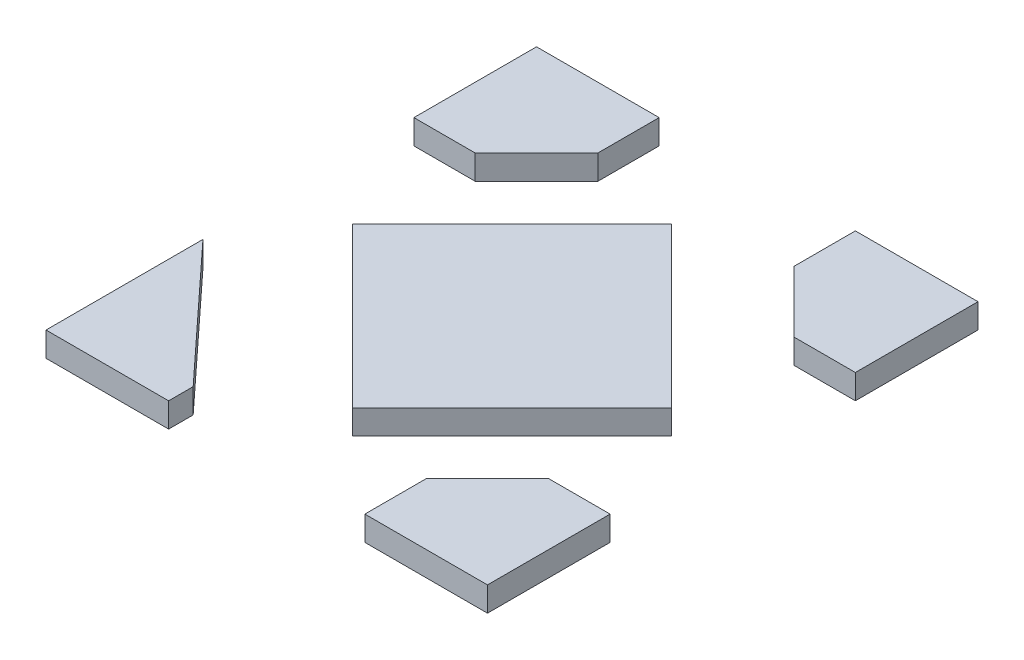
SolidWorks part; units mm, degrees
material "Latón"
ref_plane "Front" through (0, 0, 0) normal (0, 0, 1) x (1, 0, 0)
ref_plane "Top" through (0, 0, 0) normal (0, 1, 0) x (1, 0, 0)
ref_plane "Right" through (0, 0, 0) normal (1, 0, 0) x (0, 0, -1)
sketch "Croquis1" plane through (0, 0, 0) normal (0, -1, 0) x (1, 0, 0)
  line L0 (0.325, -0.6867) -> (-0.325, -0.6867) construction
  line L1 (-0.7516, 0.325) -> (-0.7516, -0.325) construction
  line L2 (-0.7516, -0.325) -> (2.8473, -0.325) construction
  line L3 (-0.7516, 0.325) -> (2.8473, 0.325) construction
  line L4 (0.325, -0.6867) -> (0.325, 1.4562) construction
  line L5 (-0.325, -0.6867) -> (-0.325, 1.4562) construction
  line L6 (0, -0.325) -> (0.325, 0)
  line L7 (0.325, 0) -> (0, 0.325)
  line L8 (0, 0.325) -> (-0.325, 0)
  line L9 (-0.325, 0) -> (0, -0.325)
  point P3 (0, -0.6867)
  point P6 (-0.7516, 0)
  dimension "D1" = 0.65
  dimension "D2" = 0.65
extrude "Saliente-Extruir1" add sketch "Croquis1" along normal blind 0.05
sketch "Croquis2" plane through (0, 0, 0) normal (0, -1, 0) x (1, 0, 0)
  line L0 (0.325, 0) -> (0.325, 0.8942) construction
  line L1 (0, 0.325) -> (0, 0.8942) construction
  line L2 (0, 0.8942) -> (0.325, 0.8942) construction
  line L4 (0.2, 0.375) -> (0.325, 0.25) construction
  line L11 (0.45, 0.25) -> (0.1506, 0.25) construction
  line L13 (0.2, 0.5) -> (0.2, 0.25) construction
  line L15 (0.2, 0.5) -> (0.45, 0.5)
  line L17 (-0.5, 0.5) -> (0.5, 0.5) construction
  line L18 (0.45, 0.5) -> (0.45, 0.25)
  line L19 (0.2, 0.5) -> (0.2, 0.375)
  line L20 (0.2, 0.375) -> (0.325, 0.25)
  line L21 (0.325, 0.25) -> (0.45, 0.25)
  point P13 (0.325, 0.5)
  point P18 (0.325, 0.5)
  dimension "D1" = 0.25
extrude "Saliente-Extruir2" add sketch "Croquis2" along normal up to surface (0.05 mm away) separate body up to face at (0, -0.05, 0)
pattern_circular "MatrizC5" count 2 every 180 about axis through (0, 0, 0) along (0, 1, 0) of bodies 102
mirror "Simetría1" about plane through (0, 0, 0) normal (0, 0, 1) of bodies 102
sketch "Croquis3" plane through (0, 0, 0) normal (0, -1, 0) x (1, 0, 0)
  line L0 (-0.325, 0) -> (-0.325, 0.9105) construction
  line L1 (-0.45, 0.5) -> (-0.2, 0.5)
  line L2 (-0.5, 0.5) -> (0.5, 0.5) construction
  line L3 (-0.45, 0.5) -> (-0.45, 0.18)
  line L4 (-0.45, 0.18) -> (-0.2, 0.18) construction
  line L5 (-0.2, 0.18) -> (-0.2, 0.45) construction
  line L6 (-0.45, 0.18) -> (-0.2, 0.45)
  line L7 (-0.2, 0.45) -> (-0.2, 0.5)
  point P8 (-0.325, 0.5)
extrude "Saliente-Extruir3" add sketch "Croquis3" along normal blind 0.05 separate body
